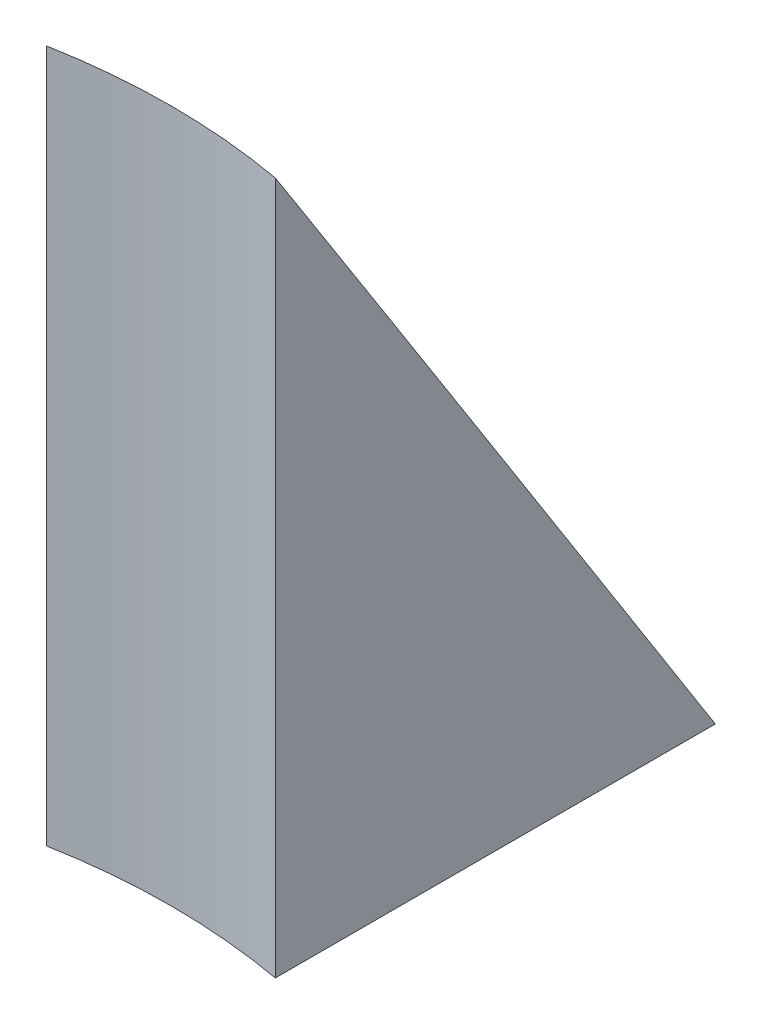
SolidWorks part; units mm, degrees
ref_plane "Front Plane" through (0, 0, 0) normal (0, 0, 1) x (1, 0, 0)
ref_plane "Top Plane" through (0, 0, 0) normal (0, 1, 0) x (1, 0, 0)
ref_plane "Right Plane" through (0, 0, 0) normal (1, 0, 0) x (0, 0, -1)
sketch "Sketch1" plane through (0, 0, 0) normal (0, 0, 1) x (1, 0, 0)
  line L0 (0, 0) -> (0, 65.7654) construction
  line L1 (44.5, 0) -> (44.5, 48.5)
  line L2 (44.5, 48.5) -> (75, 0)
  line L3 (75, 0) -> (44.5, 0)
  dimension "D1" = 48.5
  dimension "D2" = 44.5
  dimension "D3" = 75
revolve "Revolve1" add sketch "Sketch1" angle 360 about L0
sketch "Sketch2" plane through (0, 0, 0) normal (0, -1, 0) x (1, 0, 0)
  line L0 (0, 0) -> (0, -75) construction
  line L2 (-8, -28.1269) -> (8, -28.1269)
  line L3 (-8, -28.1269) -> (-8, -100.5567)
  line L4 (-8, -100.5567) -> (8, -100.5567)
  line L5 (8, -28.1269) -> (8, -100.5567)
  line L6 (-8, -28.1269) -> (8, -100.5567) construction
  line L7 (-8, -100.5567) -> (8, -28.1269) construction
  circle A0 centre (0, 0) radius 75 construction
  point P5 (0, -64.3418)
  dimension "D1" = 16
extrude "Cut-Extrude1" cut sketch "Sketch2" against normal through all flip side to cut
